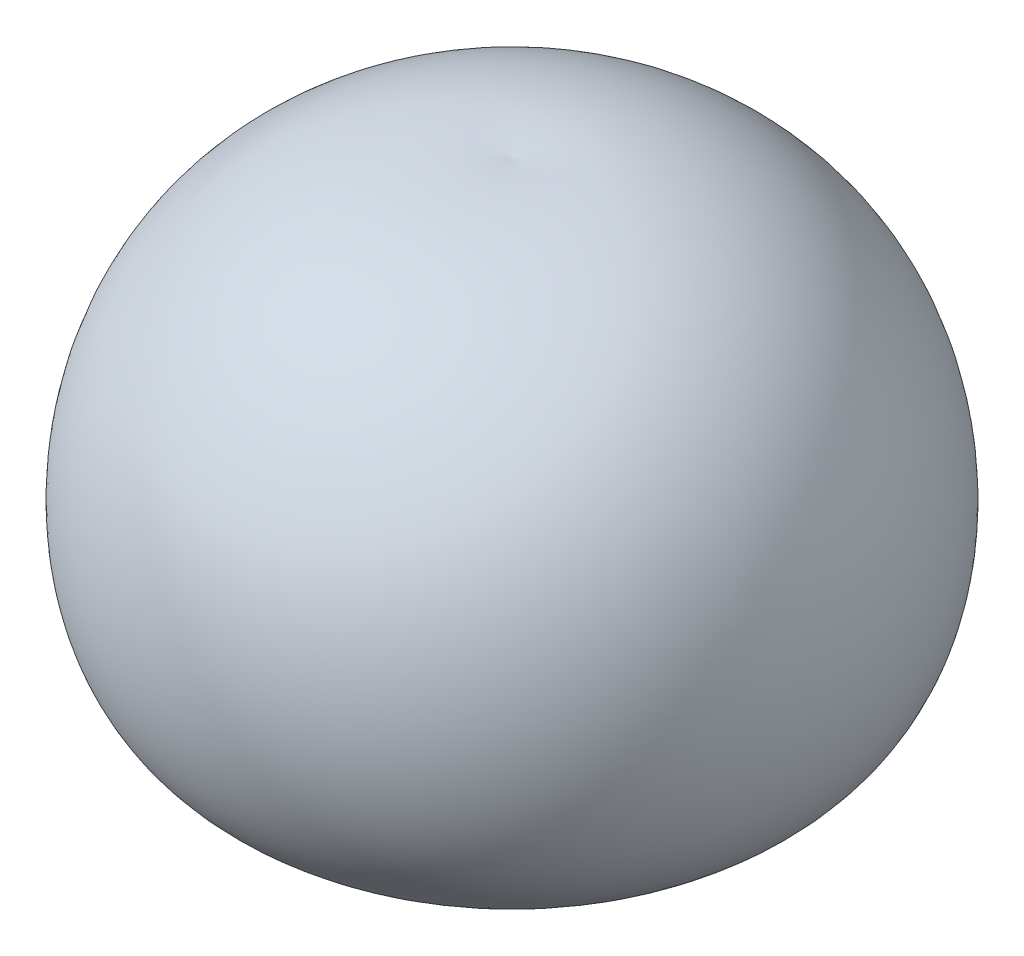
SolidWorks part; units mm, degrees
ref_plane "Alzado" through (0, 0, 0) normal (0, 0, 1) x (1, 0, 0)
ref_plane "Planta" through (0, 0, 0) normal (0, 1, 0) x (1, 0, 0)
ref_plane "Vista lateral" through (0, 0, 0) normal (1, 0, 0) x (0, 0, -1)
sketch "Croquis1" plane through (0, 0, 0) normal (0, 0, 1) x (1, 0, 0)
  line L0 (0, 0) -> (0, 57)
  line L1 (0, 28.5) -> (35.4017, 28.5)
  spline S0 degree 3 poles (0, 0) (9.3637, -1.03) (35.328, 2.4309) (37.8238, 44.073) (15.9996, 58.8337) (0, 57) knots 0 0 0 0 0.320083 0.582992 1 1 1 1
  dimension "D1" = 57
revolve "Revolución1" add sketch "Croquis1" angle 360 about L0
